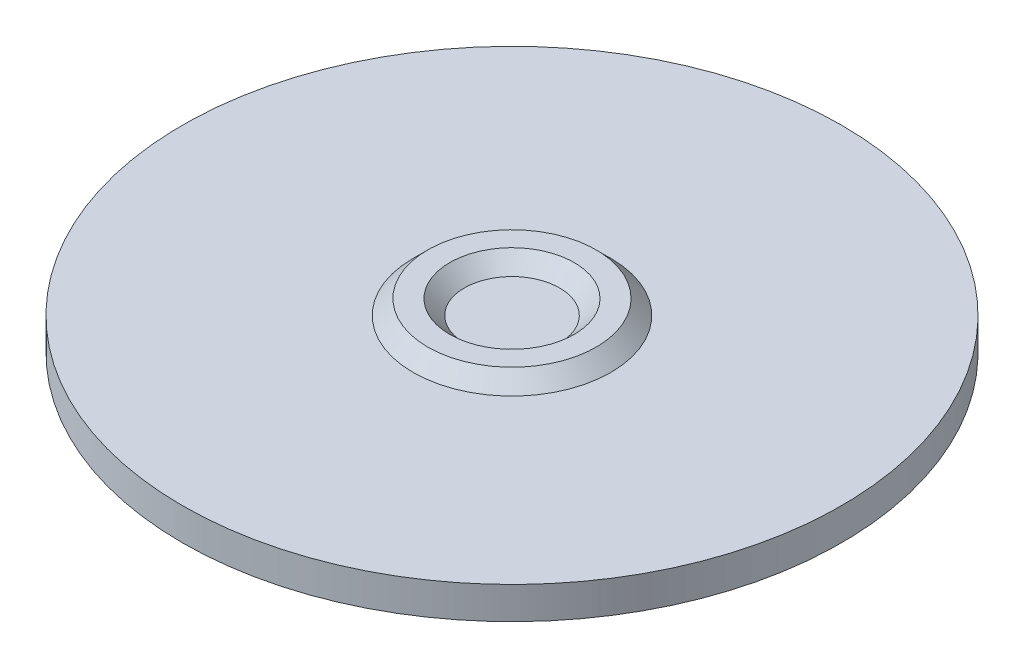
SolidWorks part; units mm, degrees
ref_plane "Front Plane" through (0, 0, 0) normal (0, 0, 1) x (1, 0, 0)
ref_plane "Top Plane" through (0, 0, 0) normal (0, 1, 0) x (1, 0, 0)
ref_plane "Right Plane" through (0, 0, 0) normal (1, 0, 0) x (0, 0, -1)
sketch "Sketch1" plane through (0, 0, 0) normal (0, 1, 0) x (1, 0, 0)
  circle A0 centre (0, 0) radius 22.5
  dimension "D1" = 45
extrude "Boss-Extrude1" add sketch "Sketch1" along normal blind 2.2
sketch "Sketch2" plane through (0, 2.2, 0) normal (0, 1, 0) x (1, 0, 0)
  circle A0 centre (0, 0) radius 6.75
  dimension "D1" = 13.5
extrude "Boss-Extrude2" add sketch "Sketch2" along normal blind 1 draft 45 separate body contours A0
sketch "Sketch3" plane through (0, 3.2, 0) normal (0, 1, 0) x (1, 0, 0)
  circle A0 centre (0, 0) radius 4.25
  dimension "D1" = 8.5
extrude "Cut-Extrude1" cut sketch "Sketch3" against normal blind 1 draft 45
